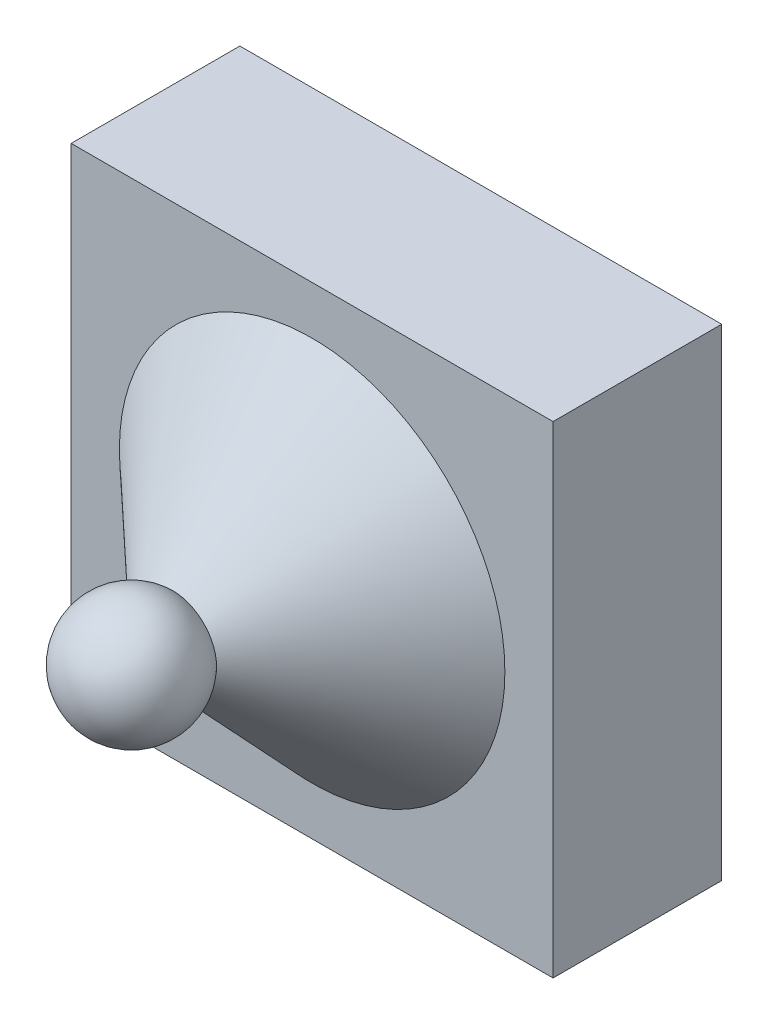
SolidWorks part; units mm, degrees
ref_plane "Front Plane" through (0, 0, 0) normal (0, 0, 1) x (1, 0, 0)
ref_plane "Top Plane" through (0, 0, 0) normal (0, 1, 0) x (1, 0, 0)
ref_plane "Right Plane" through (0, 0, 0) normal (1, 0, 0) x (0, 0, -1)
sketch "Sketch1" plane through (0, 0, 0) normal (0, 0, 1) x (1, 0, 0)
  line L1 (-50, -50) -> (50, -50)
  line L2 (-50, -50) -> (-50, 50)
  line L3 (-50, 50) -> (50, 50)
  line L4 (50, -50) -> (50, 50)
  line L5 (-50, -50) -> (50, 50) construction
  line L6 (-50, 50) -> (50, -50) construction
  point P0 (0, 0)
  dimension "D1" = 100
  dimension "D2" = 100
extrude "Boss-Extrude1" add sketch "Sketch1" along normal blind 35
sketch "Sketch2" plane through (0, 0, 0) normal (0, 1, 0) x (1, 0, 0)
  line L0 (0, -35) -> (0, -72.5)
  line L1 (40, -35) -> (9.1192, -63.9507)
  line L2 (0, -35) -> (0, -85) construction
  line L3 (0, -85) -> (0, -72.5)
  line L4 (50, 0) -> (-50, 0)
  line L5 (-50, 0) -> (-50, -35)
  line L6 (-50, -35) -> (50, -35)
  line L7 (50, -35) -> (50, 0)
  line L10 (-50, -35) -> (50, -35) construction
  line L12 (0, -35) -> (40, -35)
  arc A0 (0, -85) -> (9.1192, -63.9507) centre (0, -72.5) ccw
  point P6 (0, 0)
  dimension "D3" = 25
  dimension "D2" = 37.5
  dimension "D4" = 10
  dimension "D1" = 0
revolve "Revolve1" add sketch "Sketch2" angle 360 about L0
